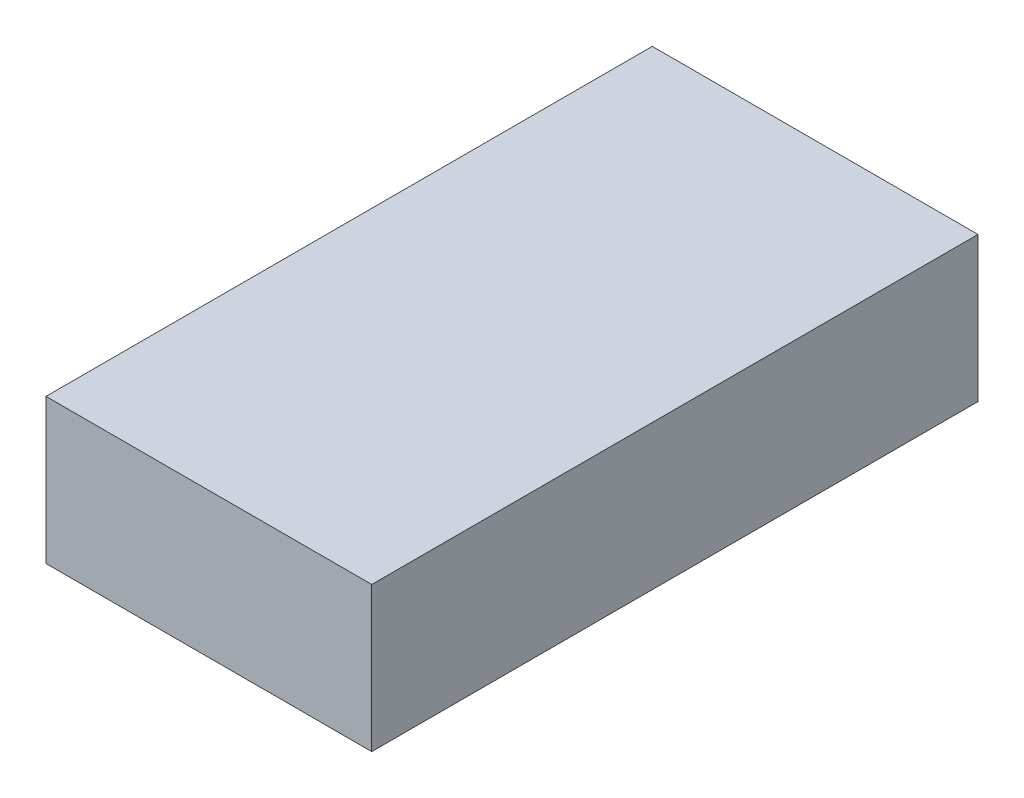
SolidWorks part; units mm, degrees
ref_plane "Front Plane" through (0, 0, 0) normal (0, 0, 1) x (1, 0, 0)
ref_plane "Top Plane" through (0, 0, 0) normal (0, 1, 0) x (1, 0, 0)
ref_plane "Right Plane" through (0, 0, 0) normal (1, 0, 0) x (0, 0, -1)
sketch "Sketch1" plane through (0, 0, 0) normal (0, 1, 0) x (1, 0, 0)
  line L1 (0, 0) -> (114.3, 0)
  line L2 (0, 0) -> (0, 212.725)
  line L3 (0, 212.725) -> (114.3, 212.725)
  line L4 (114.3, 0) -> (114.3, 212.725)
  dimension "D1" = 212.725
  dimension "D2" = 114.3
extrude "Boss-Extrude1" add sketch "Sketch1" along normal blind 50.8
